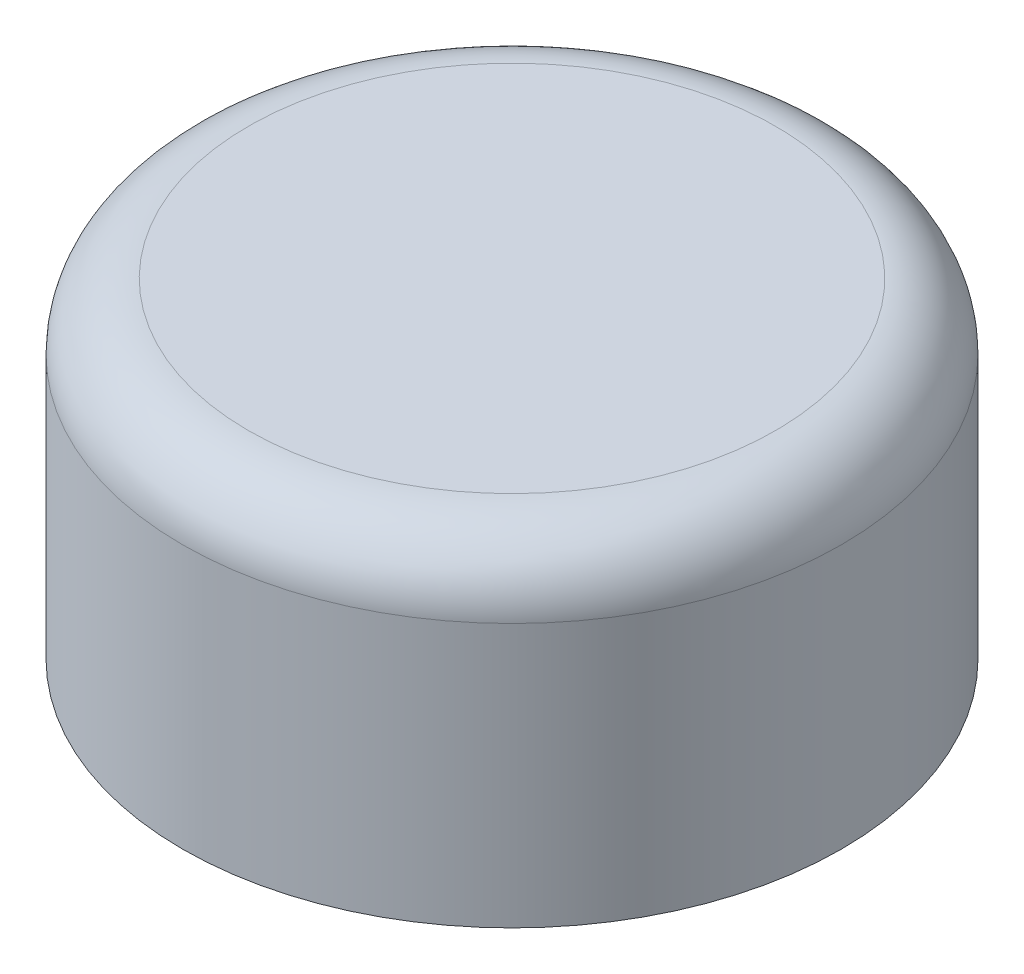
SolidWorks part; units mm, degrees
ref_plane "Спереди" through (0, 0, 0) normal (0, 0, 1) x (1, 0, 0)
ref_plane "Сверху" through (0, 0, 0) normal (0, 1, 0) x (1, 0, 0)
ref_plane "Справа" through (0, 0, 0) normal (1, 0, 0) x (0, 0, -1)
sketch "Sketch1" plane through (0, 0, 0) normal (0, 1, 0) x (1, 0, 0)
  circle A0 centre (0, 0) radius 5
  dimension "D1" = 10
extrude "Boss-Extrude1" add sketch "Sketch1" along normal blind 5
fillet "Fillet1" radius 1 1 edges at (0, 5, 5)
sketch "Sketch2" plane through (0, 0, 0) normal (0, -1, 0) x (1, 0, 0)
  circle A0 centre (0, 0) radius 3.7
  dimension "D1" = 7.4
extrude "Cut-Extrude1" cut sketch "Sketch2" against normal blind 2
